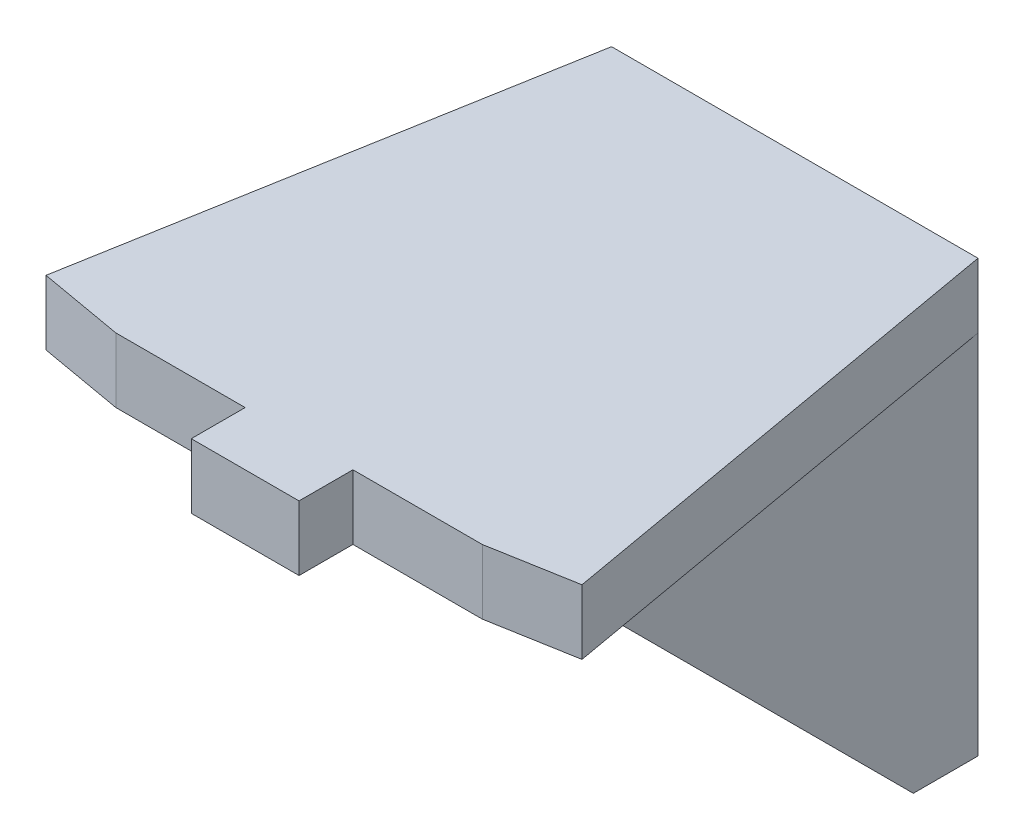
SolidWorks part; units mm, degrees
material "1060 Alloy"
ref_plane "Front Plane" through (0, 0, 0) normal (0, 0, 1) x (1, 0, 0)
ref_plane "Top Plane" through (0, 0, 0) normal (0, 1, 0) x (1, 0, 0)
ref_plane "Right Plane" through (0, 0, 0) normal (1, 0, 0) x (0, 0, -1)
sketch "Sketch1" plane through (0, 0, 0) normal (1, 0, 0) x (0, 0, -1)
  line L0 (0, 0) -> (-20, 0)
  line L1 (-20, 0) -> (-20, -3)
  line L2 (-20, -3) -> (-11.5, -11.5)
  line L3 (-11.5, -11.5) -> (0, 0) construction
  line L4 (-3, -20) -> (-11.5, -11.5)
  line L5 (0, -20) -> (-3, -20)
  line L6 (0, 0) -> (0, -20)
  dimension "D1" = 3
  dimension "D2" = 20
extrude "Boss-Extrude1" add sketch "Sketch1" along normal mid plane 17
sketch "Sketch2" plane through (0, 0, 0) normal (1, 0, 0) x (0, 0, -1)
  line L0 (-20, -3) -> (-3, -20) construction
  line L1 (-3, -3) -> (-20, -3)
  line L2 (-3, -3) -> (-3, -20)
  line L3 (-3, -20) -> (-20, -20)
  line L4 (-20, -3) -> (-20, -20)
  line L5 (-20, 0) -> (-20, -3) construction
extrude "Cut-Extrude1" cut sketch "Sketch2" against normal mid plane 12
sketch "Sketch3" plane through (0, 0, 3) normal (0, 0, 1) x (1, 0, 0)
  line L0 (0, -9) -> (0, -12) construction
  line L1 (-3, -9) -> (-3, -12)
  line L2 (3, -9) -> (3, -12)
  line L3 (0, -10.5) -> (0.7454, -10.5) construction
  line L4 (-6, -20) -> (6, -20) construction
  arc A0 (-3, -9) -> (3, -9) centre (0, -9) cw
  arc A1 (-3, -12) -> (3, -12) centre (0, -12) ccw
  dimension "D3" = 9
  dimension "D4" = 5
  dimension "D1" = 3
  dimension "D2" = 3
extrude "Cut-Extrude2" cut sketch "Sketch3" against normal up to next
sketch "Sketch4" plane through (0, 0, 0) normal (0, 0, -1) x (-1, 0, 0)
  line L0 (-1, -2.15) -> (1, -2.15) construction
  line L1 (-1, -3) -> (1, -3)
  line L2 (-1, -1.3) -> (1, -1.3)
  line L3 (0, 0) -> (0, -2.15) construction
  line L4 (-8.5, 0) -> (8.5, 0) construction
  line L5 (-2.1032, -9.8) -> (3, -9.8) construction
  line L6 (-1, -18.3) -> (1, -18.3)
  line L7 (-1, -16.6) -> (1, -16.6)
  line L8 (3, -12) -> (3, -9) construction
  arc A0 (-1, -3) -> (-1, -1.3) centre (-1, -2.15) cw
  arc A1 (1, -3) -> (1, -1.3) centre (1, -2.15) ccw
  arc A2 (1, -16.6) -> (1, -18.3) centre (1, -17.45) cw
  arc A3 (-1, -16.6) -> (-1, -18.3) centre (-1, -17.45) ccw
  dimension "D3" = 3.7
  dimension "D4" = 3
  dimension "D5" = 17
  dimension "D1" = 0.85
  dimension "D2" = 0.85
ref_plane "Plane1" through (0, 0, 0) normal (0, 0.7071, 0.7071) x (-1, 0, 0)
sketch "Esboço1" plane through (0, 0, 20) normal (0, 0, 1) x (1, 0, 0)
  line L6 (-8.5, 0) -> (-8.5, -3)
  line L7 (-8.5, -3) -> (-6, -3)
  line L8 (-6, -3) -> (6, -3)
  line L9 (6, -3) -> (8.5, -3)
  line L10 (8.5, -3) -> (8.5, 0)
  line L11 (8.5, 0) -> (-8.5, 0)
  line L12 (-8.5, 0) -> (-8.5, -3)
  line L13 (-8.5, -3) -> (-6, -3)
  line L14 (-6, -3) -> (6, -3)
  line L15 (6, -3) -> (8.5, -3)
  line L16 (8.5, -3) -> (8.5, 0)
  line L17 (8.5, 0) -> (-8.5, 0)
  dimension "D1" = 0
extrude "Ressalto-extrusão1" add sketch "Esboço1" along normal blind 3 contours L13 L14 L15 L16 L17 L12
sketch "Esboço2" plane through (0, 0, 0) normal (0, 1, 0) x (1, 0, 0)
  line L0 (-8.5, 0) -> (-12.4332, -22.3065)
  line L2 (-8.5, -23) -> (-8.5, 0)
  line L3 (-8.5, -23) -> (-12.4332, -22.3065)
extrude "Ressalto-extrusão2" add sketch "Esboço2" against normal blind 3
sketch "Esboço3" plane through (0, 0, 23) normal (0, 0, 1) x (1, 0, 0)
  line L0 (8.5, 0) -> (-8.5, 0) construction
  line L1 (-2.5, 0) -> (2.5, 0)
  line L2 (-2.5, 0) -> (-2.5, -3)
  line L3 (-2.5, -3) -> (2.5, -3)
  line L4 (2.5, 0) -> (2.5, -3)
  line L5 (-8.5, -3) -> (8.5, -3) construction
  line L9 (-8.5, 0) -> (-8.5, -3) construction
  line L10 (8.5, -3) -> (8.5, 0) construction
  dimension "D1" = 6
  dimension "D2" = 6
extrude "Ressalto-extrusão3" add sketch "Esboço3" along normal blind 2.5
mirror "Espelhar1" about plane through (0, 0, 0) normal (1, 0, 0) of "Ressalto-extrusão2"
